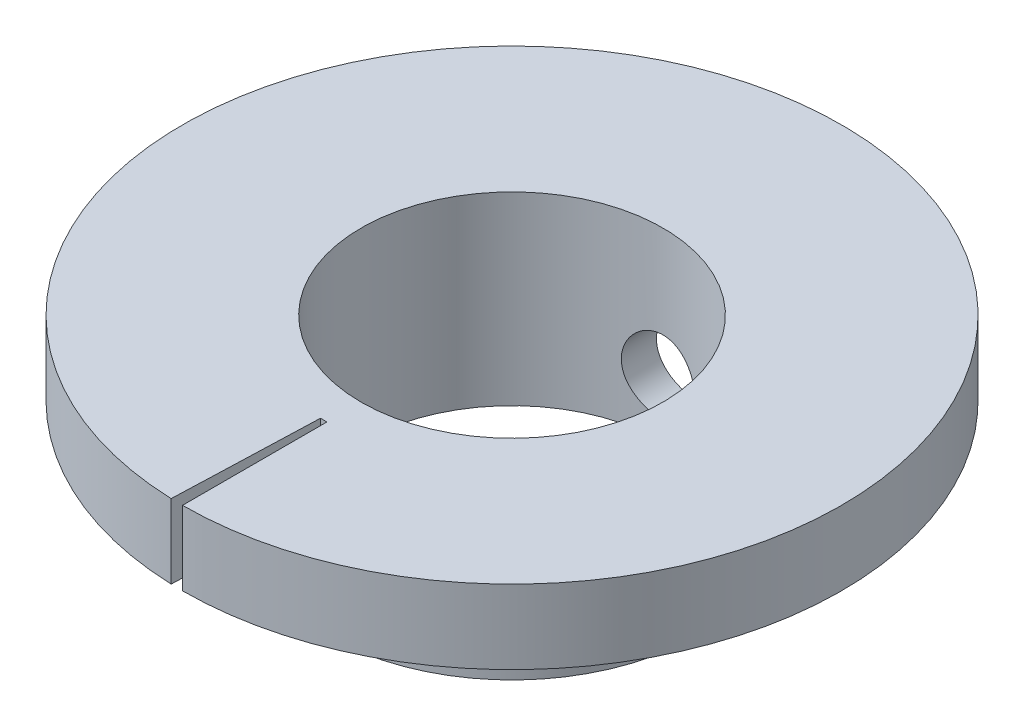
SolidWorks part; units mm, degrees
ref_plane "Front Plane" through (0, 0, 0) normal (0, 0, 1) x (1, 0, 0)
ref_plane "Top Plane" through (0, 0, 0) normal (0, 1, 0) x (1, 0, 0)
ref_plane "Right Plane" through (0, 0, 0) normal (1, 0, 0) x (0, 0, -1)
sketch "Sketch1" plane through (0, 0, 0) normal (0, 1, 0) x (1, 0, 0)
  circle A0 centre (0, 0) radius 4
  circle A1 centre (0, 0) radius 8.9
  dimension "D1" = 17.8
  dimension "D2" = 8
extrude "Boss-Extrude1" add sketch "Sketch1" along normal blind 2
sketch "Sketch2" plane through (0, 2, 0) normal (0, 1, 0) x (1, 0, 0)
  line L0 (0, 0) -> (0, -10.526)
  line L1 (0, -10.526) -> (-0.3554, -10.1774)
  line L2 (-0.3554, -10.1774) -> (0, 0)
  point P2 (-0.3554, -10.1774)
  point P5 (0, -10.526)
  dimension "D1" = 2
extrude "Cut-Extrude1" cut sketch "Sketch2" against normal blind 2
sketch "Sketch3" plane through (0, 2, 0) normal (0, 1, 0) x (1, 0, 0)
  circle A0 centre (0, 0) radius 4
  circle A1 centre (0, 0) radius 5
  dimension "D1" = 10
extrude "Boss-Extrude2" add sketch "Sketch3" against normal blind 5
sketch "Sketch4" plane through (0, 2, 0) normal (0, 1, 0) x (1, 0, 0)
  circle A0 centre (0, 0) radius 4.075
  dimension "D1" = 8.15
extrude "Cut-Extrude2" cut sketch "Sketch4" against normal blind 15
sketch "Sketch6" plane through (0, 0, 0) normal (0, 0, 1) x (1, 0, 0)
  line L0 (-8.9, 0) -> (8.9, 0) construction
  circle A0 centre (0, -1.5) radius 1
  dimension "D2" = 2
  dimension "D1" = 1.5
extrude "Cut-Extrude3" cut sketch "Sketch6" against normal blind 15
